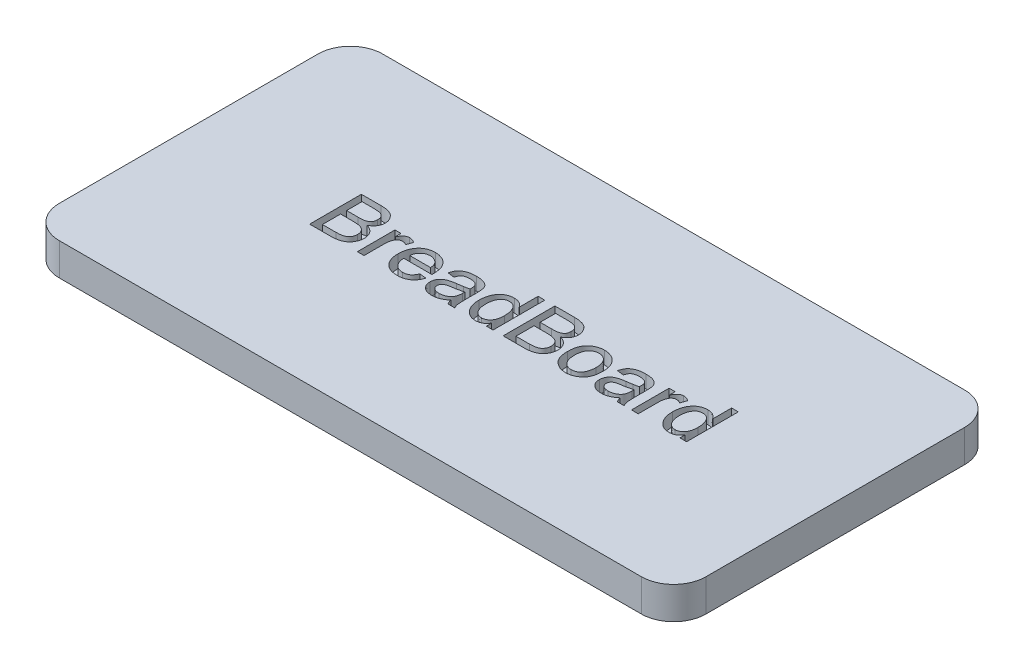
SolidWorks part; units mm, degrees
ref_plane "前视基准面" through (0, 0, 0) normal (0, 0, 1) x (1, 0, 0)
ref_plane "上视基准面" through (0, 0, 0) normal (0, 1, 0) x (1, 0, 0)
ref_plane "右视基准面" through (0, 0, 0) normal (1, 0, 0) x (0, 0, -1)
other "Configuration Table"
sketch "草图1" plane through (0, 0, 0) normal (0, 1, 0) x (1, 0, 0)
  line L1 (-45, 25) -> (45, 25)
  line L2 (-50, 20) -> (-50, -20)
  line L3 (-45, -25) -> (45, -25)
  line L4 (50, 20) -> (50, -20)
  line L5 (-50, 25) -> (50, -25) construction
  line L6 (-50, -25) -> (50, 25) construction
  arc A0 (-50, -20) -> (-45, -25) centre (-45, -20) ccw
  arc A1 (45, -25) -> (50, -20) centre (45, -20) ccw
  arc A2 (45, 25) -> (50, 20) centre (45, 20) cw
  arc A3 (-45, 25) -> (-50, 20) centre (-45, 20) ccw
  point P0 (0, 0)
  dimension "D3" = 5
  dimension "D1" = 100
  dimension "D2" = 50
extrude "凸台-拉伸1" add sketch "草图1" along normal blind 5
sketch "草图2" plane through (0, 5, 0) normal (0, 1, 0) x (1, 0, 0)
  text T0 "BreadBoard" font "@Arial Unicode MS" height 8
  point P1 (-26.4039, -1.9751)
  point P2 (-33.3687, -3.5344)
  point P3 (0, 0)
  point P4 (-28.6909, -3.4304)
extrude "切除-拉伸1" cut sketch "草图2" against normal blind 2
